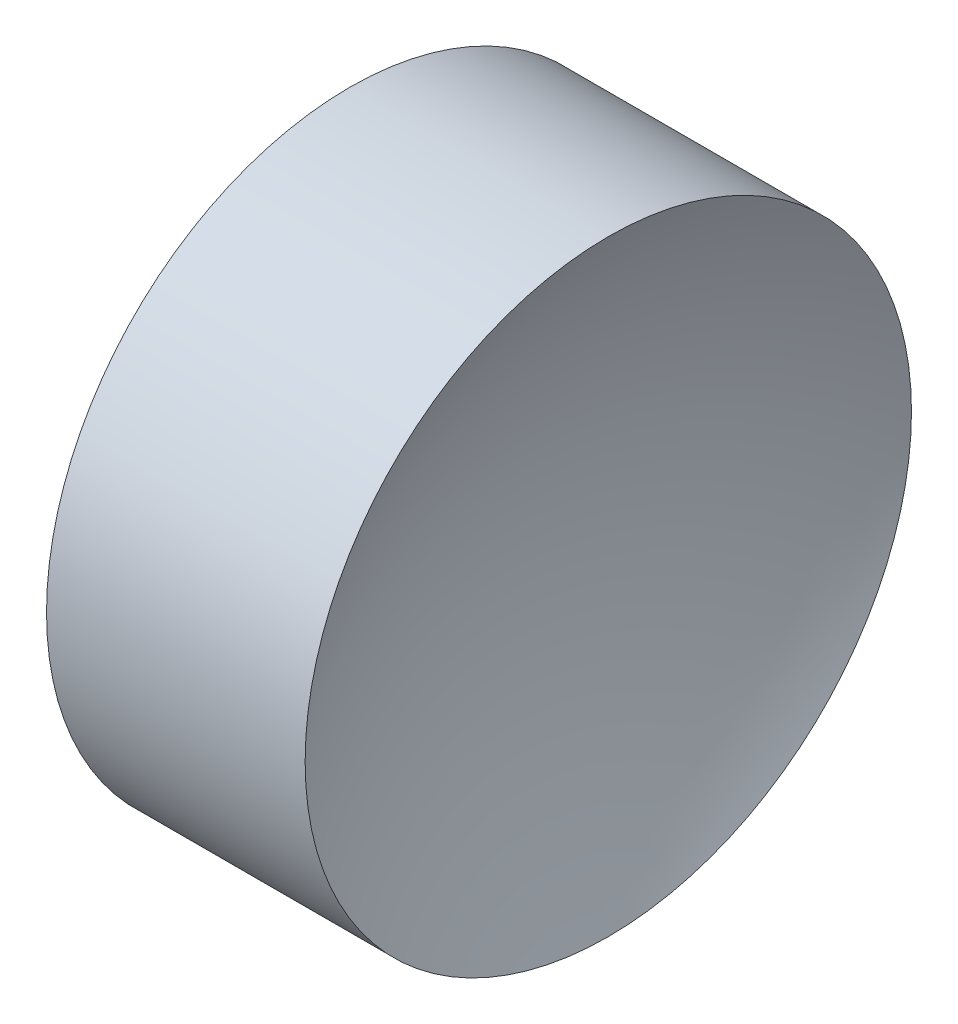
SolidWorks part; units mm, degrees
ref_plane "前视基准面" through (0, 0, 0) normal (0, 0, 1) x (1, 0, 0)
ref_plane "上视基准面" through (0, 0, 0) normal (0, 1, 0) x (1, 0, 0)
ref_plane "右视基准面" through (0, 0, 0) normal (1, 0, 0) x (0, 0, -1)
sketch "草图1" plane through (0, 0, 0) normal (0, 0, 1) x (1, 0, 0)
  line L0 (42.4499, 26.089) -> (55.6645, 26.089) construction
  line L1 (46.8452, 26.089) -> (49.2452, 26.089)
  line L3 (48.0452, 32.439) -> (50.7536, 32.439)
  line L4 (48.0452, 32.439) -> (45.3368, 32.439)
  arc A0 (46.8452, 26.089) -> (45.3368, 32.439) centre (32.7252, 26.089) ccw
  arc A1 (50.7536, 32.439) -> (49.2452, 26.089) centre (63.3652, 26.089) ccw
revolve "旋转1" add sketch "草图1" angle 360 about L0
